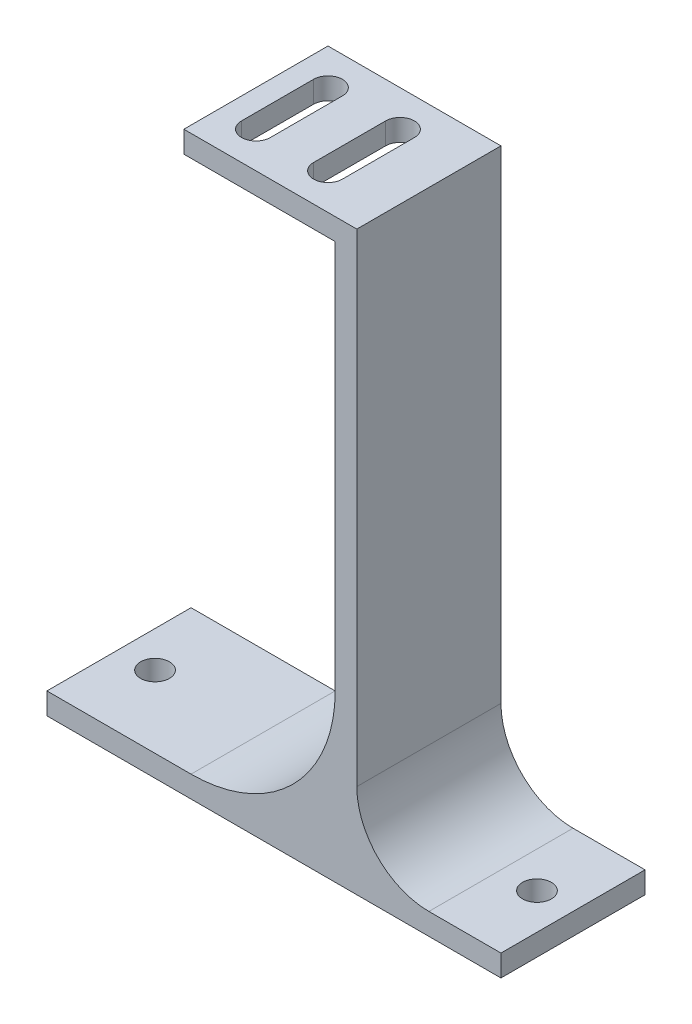
SolidWorks part; units mm, degrees
ref_plane "Plan de face" through (0, 0, 0) normal (0, 0, 1) x (1, 0, 0)
ref_plane "Plan de dessus" through (0, 0, 0) normal (0, 1, 0) x (1, 0, 0)
ref_plane "Plan de droite" through (0, 0, 0) normal (1, 0, 0) x (0, 0, -1)
sketch "Esquisse1" plane through (0, 0, 0) normal (0, 0, 1) x (1, 0, 0)
  line L0 (43, 3) -> (63, 3)
  line L1 (0, 0) -> (63, 0)
  line L2 (0, 0) -> (0, 3)
  line L3 (0, 3) -> (40, 3)
  line L4 (63, 0) -> (63, 3)
  line L6 (40, 3) -> (40, 77)
  line L8 (43, 3) -> (43, 80)
  line L11 (40, 77) -> (19, 77)
  line L12 (19, 80) -> (19, 77)
  line L13 (19, 80) -> (43, 80)
  line L14 (40, 3) -> (43, 3) construction
  point P7 (41.5, 3)
  point P15 (19, 78.5)
  dimension "D1" = 63
  dimension "D2" = 3
  dimension "D3" = 3
  dimension "D4" = 3
  dimension "D5" = 80
  dimension "D6" = 21
  dimension "D7" = 41.5
  dimension "D8" = 20
extrude "Boss.-Extru.1" add sketch "Esquisse1" along normal blind 20
sketch "Esquisse2" plane through (0, 80, 0) normal (0, 1, 0) x (1, 0, 0)
  line L0 (24, -5) -> (24, -15) construction
  line L1 (26, -5) -> (26, -15)
  line L2 (22, -5) -> (22, -15)
  line L3 (34, -5) -> (34, -15) construction
  line L4 (36, -5) -> (36, -15)
  line L5 (32, -5) -> (32, -15)
  line L6 (34, -10) -> (24, -10) construction
  line L8 (19, -20) -> (19, 0) construction
  arc A0 (26, -5) -> (22, -5) centre (24, -5) ccw
  arc A1 (22, -15) -> (26, -15) centre (24, -15) ccw
  arc A2 (36, -5) -> (32, -5) centre (34, -5) ccw
  arc A3 (32, -15) -> (36, -15) centre (34, -15) ccw
  point P2 (24, -10)
  point P7 (34, -10)
  point P18 (0, 0)
  point P20 (19, -10)
  dimension "D3" = 2
  dimension "D4" = 2
  dimension "D1" = 10
  dimension "D2" = 10
  dimension "D5" = 10
  dimension "D6" = 5
extrude "Enlèv. mat.-Extru.1" cut sketch "Esquisse2" against normal up to surface (3 mm away) up to face at (29.5, 77, 10)
fillet "Congé1" radius 20 1 edges at (40, 3, 10)
fillet "Congé2" radius 10 1 edges at (43, 3, 10)
sketch "Esquisse3" plane through (0, 3, 0) normal (0, 1, 0) x (1, 0, 0)
  line L0 (63, -20) -> (63, 0) construction
  line L1 (0, -20) -> (0, 0) construction
  circle A0 centre (5, -10) radius 2
  circle A1 centre (58, -10) radius 2
  point P6 (63, -10)
  dimension "D1" = 4
  dimension "D2" = 5
  dimension "D3" = 5
extrude "Enlèv. mat.-Extru.2" cut sketch "Esquisse3" against normal up to surface (3 mm away) up to face at (31.5, 0, 10)
